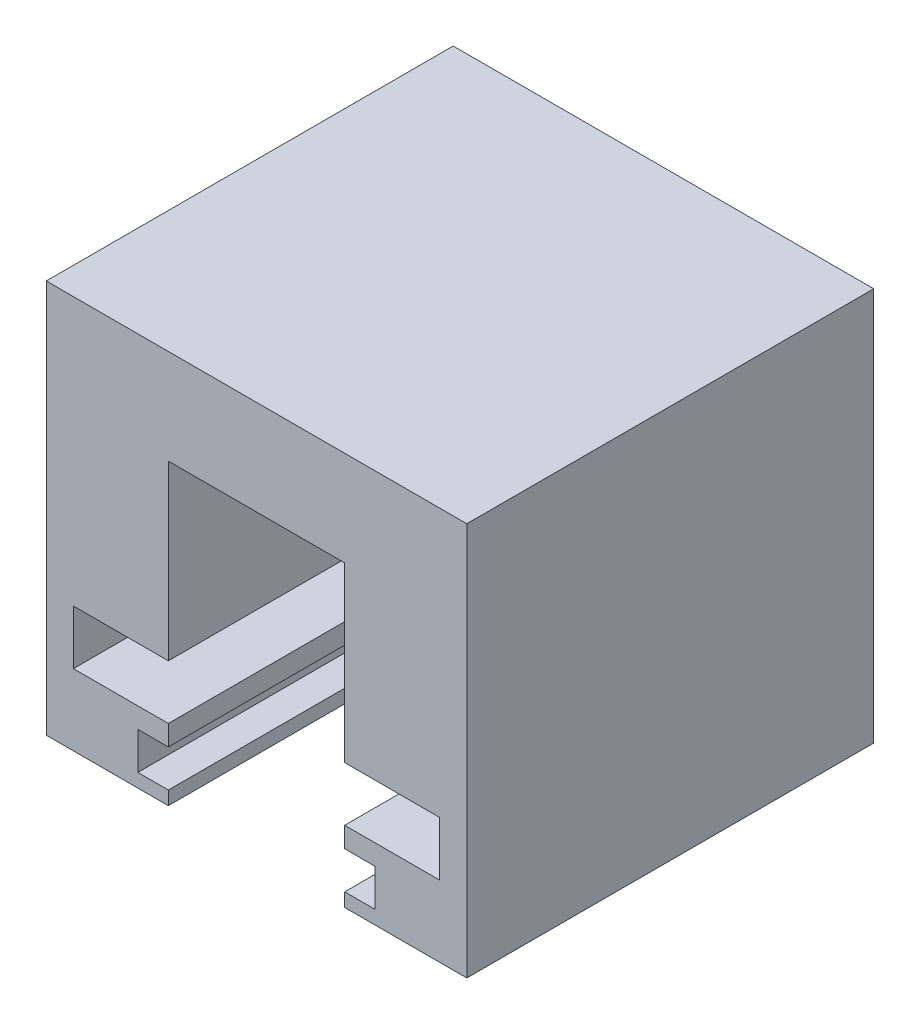
SolidWorks part; units mm, degrees
ref_plane "Front Plane" through (0, 0, 0) normal (0, 0, 1) x (1, 0, 0)
ref_plane "Top Plane" through (0, 0, 0) normal (0, 1, 0) x (1, 0, 0)
ref_plane "Right Plane" through (0, 0, 0) normal (1, 0, 0) x (0, 0, -1)
sketch "Sketch1" plane through (0, 0, 0) normal (0, 0, 1) x (1, 0, 0)
  line L0 (-31, 0) -> (-31, 29)
  line L1 (-31, 29) -> (0, 29)
  line L2 (0, 29) -> (0, 0)
  line L3 (0, 0) -> (-9, 0)
  line L4 (-9, 0) -> (-9, 22)
  line L5 (-9, 22) -> (-22, 22)
  line L6 (-22, 22) -> (-22, 0)
  line L7 (-22, 0) -> (-31, 0)
  line L8 (-22, 1) -> (-24.25, 1)
  line L9 (-24.25, 1) -> (-24.25, 3.75)
  line L10 (-24.25, 3.75) -> (-22, 3.75)
  line L11 (-22, 5.25) -> (-29, 5.25)
  line L12 (-29, 5.25) -> (-29, 9.25)
  line L13 (-29, 9.25) -> (-22, 9.25)
  line L14 (-9, 1) -> (-6.75, 1)
  line L15 (-6.75, 1) -> (-6.75, 3.75)
  line L16 (-6.75, 3.75) -> (-9, 3.75)
  line L17 (-9, 5.25) -> (-2, 5.25)
  line L18 (-2, 5.25) -> (-2, 9.25)
  line L19 (-2, 9.25) -> (-9, 9.25)
  line L20 (-22, 0) -> (-21.75, 0)
  line L21 (-21.75, 0) -> (-21.75, 1)
  line L22 (-21.75, 1) -> (-22, 1)
  line L23 (-9, 0) -> (-9.25, 0)
  line L24 (-9.25, 0) -> (-9.25, 1)
  line L25 (-9.25, 1) -> (-9, 1)
  dimension "D1" = 31
  dimension "D2" = 9
  dimension "D3" = 29
  dimension "D4" = 7
  dimension "D5" = 1
  dimension "D6" = 2.75
  dimension "D7" = 1.5
  dimension "D8" = 4
  dimension "D9" = 2.25
  dimension "D10" = 7
  dimension "D11" = 1
  dimension "D12" = 1.5
  dimension "D13" = 0
  dimension "D14" = 0.25
extrude "Boss-Extrude2" add sketch "Sketch1" along normal blind 30 contours L19 L18 L17 L4 L16 L15 L14 L3 L2 L1 L0 L7 L6 L8 L9 L10 L11 L12 L13 L5
